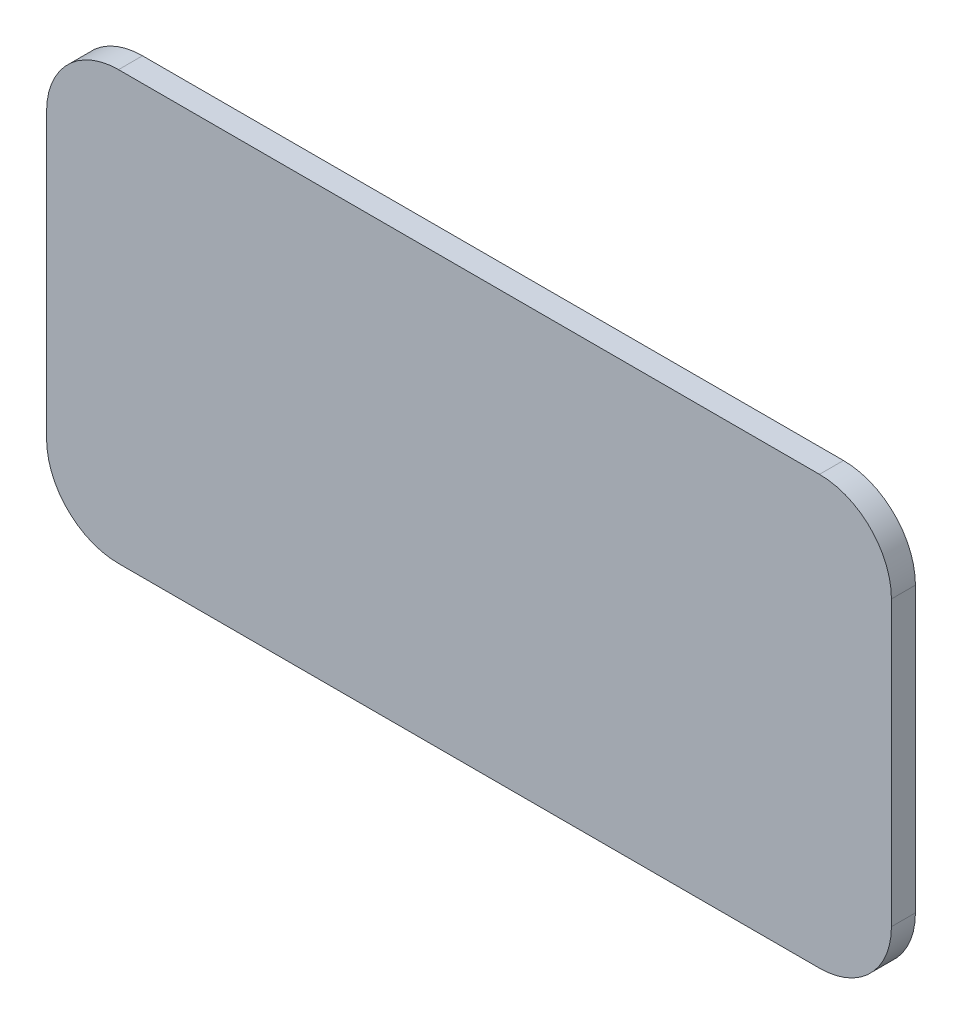
SolidWorks part; units mm, degrees
material "PC High Viscosity"
ref_plane "Front Plane" through (0, 0, 0) normal (0, 0, 1) x (1, 0, 0)
ref_plane "Top Plane" through (0, 0, 0) normal (0, 1, 0) x (1, 0, 0)
ref_plane "Right Plane" through (0, 0, 0) normal (1, 0, 0) x (0, 0, -1)
sketch "Sketch1" plane through (0, 0, 0) normal (0, 0, 1) x (1, 0, 0)
  line L8 (-238.35, -11) -> (-62.9918, -11)
  line L9 (-44.9918, 7) -> (-44.9918, 78)
  line L10 (-62.9918, 96) -> (-238.35, 96)
  line L11 (-256.35, 78) -> (-256.35, 7)
  line L12 (-238.35, -11) -> (-62.9918, -11)
  line L13 (-44.9918, 7) -> (-44.9918, 78)
  line L14 (-62.9918, 96) -> (-238.35, 96)
  line L15 (-256.35, 78) -> (-256.35, 7)
  arc A8 (-62.9918, -11) -> (-44.9918, 7) centre (-62.9918, 7) ccw
  arc A9 (-44.9918, 78) -> (-62.9918, 96) centre (-62.9918, 78) ccw
  arc A10 (-238.35, 96) -> (-256.35, 78) centre (-238.35, 78) ccw
  arc A11 (-256.35, 7) -> (-238.35, -11) centre (-238.35, 7) ccw
  arc A12 (-62.9918, -11) -> (-44.9918, 7) centre (-62.9918, 7) ccw
  arc A13 (-44.9918, 78) -> (-62.9918, 96) centre (-62.9918, 78) ccw
  arc A14 (-238.35, 96) -> (-256.35, 78) centre (-238.35, 78) ccw
  arc A15 (-256.35, 7) -> (-238.35, -11) centre (-238.35, 7) ccw
  dimension "D1" = 8
extrude "Boss-Extrude1" add sketch "Sketch1" along normal blind 6
